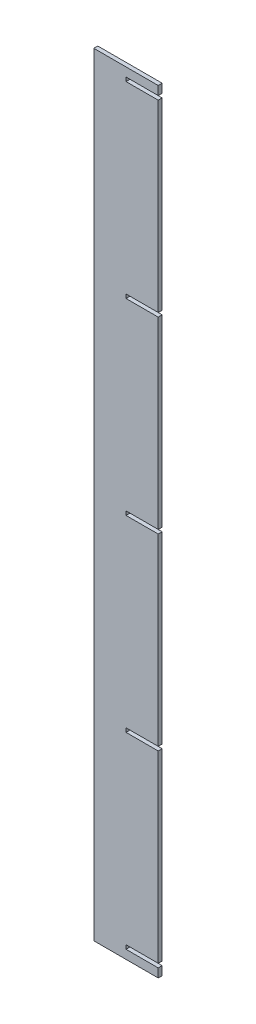
SolidWorks part; units mm, degrees
material "Oak"
ref_plane "Front Plane" through (0, 0, 0) normal (0, 0, 1) x (1, 0, 0)
ref_plane "Top Plane" through (0, 0, 0) normal (0, 1, 0) x (1, 0, 0)
ref_plane "Right Plane" through (0, 0, 0) normal (1, 0, 0) x (0, 0, -1)
sketch "Sketch1" plane through (0, 0, 0) normal (0, 0, 1) x (1, 0, 0)
  line L0 (25084.5465, 6999.9516) -> (25236.9465, 6999.9516)
  line L1 (25236.9465, 6999.9516) -> (25236.9465, 8828.7516)
  line L2 (25236.9465, 8828.7516) -> (25084.5465, 8828.7516)
  line L3 (25084.5465, 8828.7516) -> (25084.5465, 6999.9516)
  line L4 (25160.7465, 7909.6526) -> (25236.9465, 7909.6526)
  line L5 (25236.9465, 7909.6526) -> (25236.9465, 7919.0506)
  line L6 (25236.9465, 7919.0506) -> (25160.7465, 7919.0506)
  line L7 (25160.7465, 7919.0506) -> (25160.7465, 7909.6526)
  line L8 (25160.7465, 8354.1526) -> (25236.9465, 8354.1526)
  line L9 (25236.9465, 8354.1526) -> (25236.9465, 8363.5506)
  line L10 (25236.9465, 8363.5506) -> (25160.7465, 8363.5506)
  line L11 (25160.7465, 8363.5506) -> (25160.7465, 8354.1526)
  line L12 (25160.7465, 7465.1526) -> (25236.9465, 7465.1526)
  line L13 (25236.9465, 7465.1526) -> (25236.9465, 7474.5506)
  line L14 (25236.9465, 7474.5506) -> (25160.7465, 7474.5506)
  line L15 (25160.7465, 7474.5506) -> (25160.7465, 7465.1526)
  line L16 (25160.7465, 8798.6526) -> (25236.9465, 8798.6526)
  line L17 (25236.9465, 8798.6526) -> (25236.9465, 8808.0506)
  line L18 (25236.9465, 8808.0506) -> (25160.7465, 8808.0506)
  line L19 (25160.7465, 8808.0506) -> (25160.7465, 8798.6526)
  line L20 (25160.7465, 7020.6526) -> (25236.9465, 7020.6526)
  line L21 (25236.9465, 7020.6526) -> (25236.9465, 7030.0506)
  line L22 (25236.9465, 7030.0506) -> (25160.7465, 7030.0506)
  line L23 (25160.7465, 7030.0506) -> (25160.7465, 7020.6526)
extrude "Boss-Extrude1" add sketch "Sketch1" along normal blind 9.398 contours L23 L22 L1 L12 L15 L14 L4 L7 L6 L8 L11 L10 L16 L19 L18 L2 L3 L0 L20
